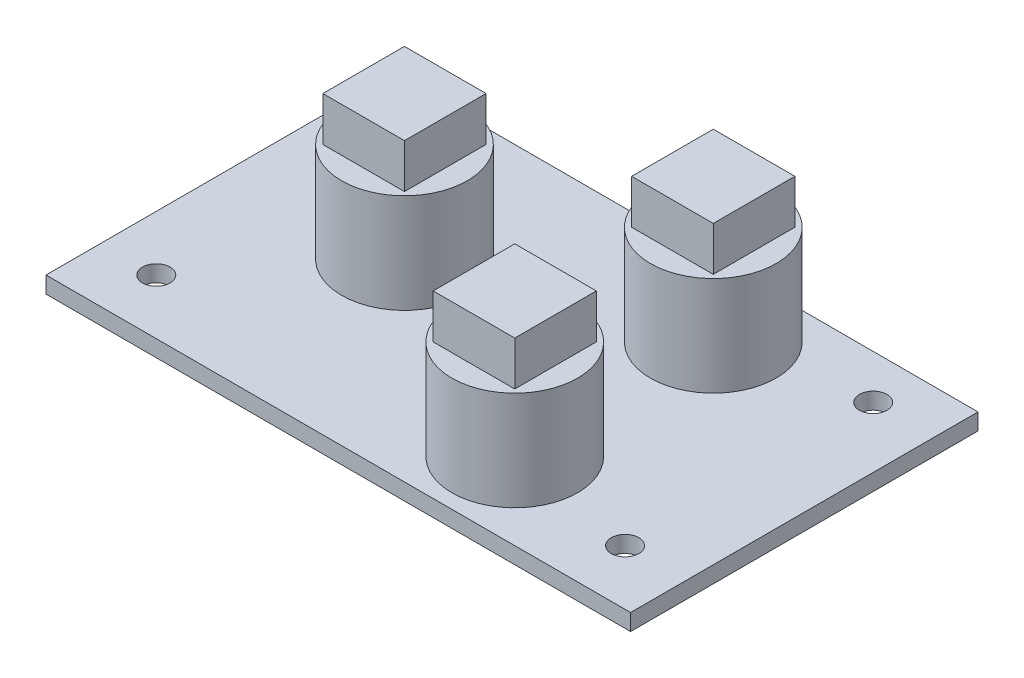
SolidWorks part; units mm, degrees
ref_plane "Piano frontale" through (0, 0, 0) normal (0, 0, 1) x (1, 0, 0)
ref_plane "Piano superiore" through (0, 0, 0) normal (0, 1, 0) x (1, 0, 0)
ref_plane "Piano destro" through (0, 0, 0) normal (1, 0, 0) x (0, 0, -1)
sketch "Schizzo1" plane through (0, 0, 0) normal (0, 1, 0) x (1, 0, 0)
  line L1 (26.5, -15.75) -> (-26.5, -15.75)
  line L2 (26.5, -15.75) -> (26.5, 15.75)
  line L3 (26.5, 15.75) -> (-26.5, 15.75)
  line L4 (-26.5, -15.75) -> (-26.5, 15.75)
  line L5 (26.5, -15.75) -> (-26.5, 15.75) construction
  line L6 (26.5, 15.75) -> (-26.5, -15.75) construction
  point P0 (0, 0)
  dimension "D1" = 31.5
  dimension "D2" = 53
extrude "Estrusione-Estrusione1" add sketch "Schizzo1" along normal blind 1.5
sketch "Schizzo2" plane through (0, 1.5, 0) normal (0, 1, 0) x (1, 0, 0)
  line L0 (-26.5, 15.75) -> (-26.5, -15.75) construction
  line L1 (26.5, 15.75) -> (-26.5, 15.75) construction
  line L2 (-21.5, 11.75) -> (26.5, 11.75) construction
  line L3 (26.5, -15.75) -> (26.5, 15.75) construction
  line L4 (21, 11.75) -> (21, -15.75) construction
  line L5 (-26.5, -15.75) -> (26.5, -15.75) construction
  line L6 (21, -10.75) -> (-26.5, -10.75) construction
  line L7 (-21.5, 11.75) -> (-21.5, -10.75) construction
  circle A0 centre (-21.5, 11.75) radius 1.25
  circle A1 centre (21, 11.75) radius 1.25
  circle A2 centre (21, -10.75) radius 1.25
  circle A3 centre (-21.5, -10.75) radius 1.25
  dimension "D1" = 2.5
  dimension "D4" = 2.5
  dimension "D6" = 2.5
  dimension "D8" = 2.5
  dimension "D2" = 5
  dimension "D3" = 4
  dimension "D5" = 42.5
  dimension "D7" = 22.5
extrude "Taglio-Estrusione1" cut sketch "Schizzo2" against normal blind 1.5
sketch "Schizzo3" plane through (0, 1.5, 0) normal (0, 1, 0) x (1, 0, 0)
  line L0 (26.5, 15.75) -> (-26.5, 15.75) construction
  line L2 (-26.5, 15.75) -> (-26.5, -15.75) construction
  circle A0 centre (-11.5, 1.75) radius 5.7
  circle A1 centre (9, -8.75) radius 5.7
  circle A2 centre (9, 9.25) radius 5.7
  dimension "D1" = 11.4
  dimension "D2" = 11.4
  dimension "D3" = 11.4
  dimension "D4" = 14
  dimension "D5" = 15
  dimension "D6" = 6.5
  dimension "D7" = 18
  dimension "D8" = 20.5
extrude "Estrusione-Estrusione2" add sketch "Schizzo3" along normal blind 9
sketch "Schizzo4" plane through (0, 10.5, 0) normal (0, 1, 0) x (1, 0, 0)
  line L0 (9, 9.25) -> (9, -8.75) construction
  line L1 (-11.5, 1.75) -> (-11.5, 7.45) construction
  line L3 (-7.8, -1.95) -> (-15.2, -1.95)
  line L4 (-7.8, -1.95) -> (-7.8, 5.45)
  line L5 (-7.8, 5.45) -> (-15.2, 5.45)
  line L6 (-15.2, -1.95) -> (-15.2, 5.45)
  line L7 (-7.8, -1.95) -> (-15.2, 5.45) construction
  line L8 (-7.8, 5.45) -> (-15.2, -1.95) construction
  line L9 (12.7, 5.55) -> (5.3, 5.55)
  line L10 (12.7, 5.55) -> (12.7, 12.95)
  line L11 (12.7, 12.95) -> (5.3, 12.95)
  line L12 (5.3, 5.55) -> (5.3, 12.95)
  line L13 (12.7, 5.55) -> (5.3, 12.95) construction
  line L14 (12.7, 12.95) -> (5.3, 5.55) construction
  line L15 (12.7, -12.45) -> (5.3, -12.45)
  line L16 (12.7, -12.45) -> (12.7, -5.05)
  line L17 (12.7, -5.05) -> (5.3, -5.05)
  line L18 (5.3, -12.45) -> (5.3, -5.05)
  line L19 (12.7, -12.45) -> (5.3, -5.05) construction
  line L20 (12.7, -5.05) -> (5.3, -12.45) construction
  circle A0 centre (-11.5, 1.75) radius 5.7 construction
  dimension "D1" = 7.4
  dimension "D2" = 7.4
  dimension "D3" = 7.4
  dimension "D4" = 7.4
  dimension "D5" = 7.4
  dimension "D6" = 7.4
extrude "Estrusione-Estrusione3" add sketch "Schizzo4" along normal blind 4
